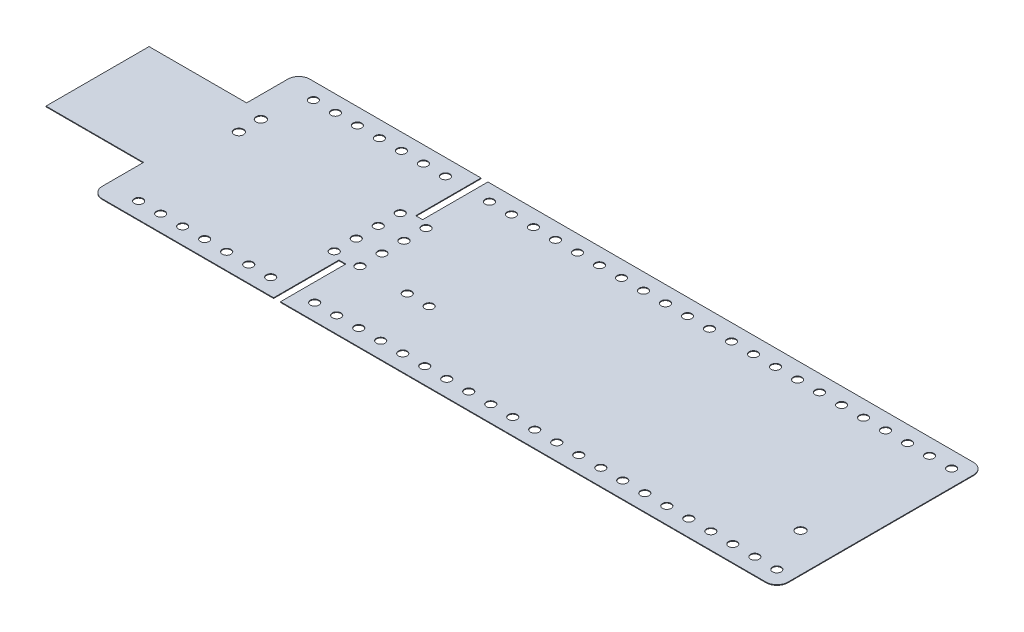
SolidWorks part; units mm, degrees
ref_plane "Front Plane" through (0, 0, 0) normal (0, 0, 1) x (1, 0, 0)
ref_plane "Top Plane" through (0, 0, 0) normal (0, 1, 0) x (1, 0, 0)
ref_plane "Right Plane" through (0, 0, 0) normal (1, 0, 0) x (0, 0, -1)
sketch "Sketch1" plane through (0, 0, 0) normal (0, 1, 0) x (1, 0, 0)
  line L0 (91.11, -12.065) -> (11.35, -12.065)
  line L1 (11.35, -5.995) -> (0, -5.995)
  line L3 (11.35, 5.995) -> (0, 5.995)
  line L4 (0, -5.995) -> (0, 5.995)
  line L5 (11.35, -5.995) -> (0, 5.995) construction
  line L6 (11.35, 5.995) -> (0, -5.995) construction
  line L7 (91.11, -12.065) -> (91.11, 12.065)
  line L8 (11.35, -12.065) -> (11.35, -5.995)
  line L9 (91.11, 12.065) -> (11.35, 12.065)
  line L10 (91.11, -12.065) -> (11.35, 12.065) construction
  line L11 (11.35, -12.065) -> (91.11, 12.065) construction
  line L12 (11.35, 5.995) -> (11.35, 12.065)
  point P0 (5.675, 0)
  point P7 (51.23, 0)
  dimension "D1" = 79.76
  dimension "D2" = 24.13
  dimension "D3" = 11.35
  dimension "D4" = 11.99
extrude "Boss-Extrude1" add sketch "Sketch1" along normal mid plane 0.0787
sketch "Sketch2" plane through (0, 0.0394, 0) normal (0, 1, 0) x (1, 0, 0)
  line L0 (11.35, 10.165) -> (91.11, 10.165) construction
  line L1 (91.11, 12.065) -> (11.35, 12.065) construction
  line L2 (91.11, -12.065) -> (91.11, 12.065) construction
  line L3 (2.5568, -8.5055) -> (57.273, -8.5055) construction
  line L4 (11.35, 12.065) -> (11.35, 5.995) construction
  circle A0 centre (14.95, 10.165) radius 0.5
  circle A1 centre (17.51, 10.165) radius 0.5
  circle A2 centre (20.07, 10.165) radius 0.5
  circle A3 centre (22.63, 10.165) radius 0.5
  circle A4 centre (25.19, 10.165) radius 0.5
  circle A5 centre (27.75, 10.165) radius 0.5
  circle A6 centre (30.31, 10.165) radius 0.5
  circle A7 centre (32.87, 10.165) radius 0.5 [skipped]
  circle A8 centre (35.43, 10.165) radius 0.5
  circle A9 centre (37.99, 10.165) radius 0.5
  circle A10 centre (40.55, 10.165) radius 0.5
  circle A11 centre (43.11, 10.165) radius 0.5
  circle A12 centre (45.67, 10.165) radius 0.5
  circle A13 centre (48.23, 10.165) radius 0.5
  circle A14 centre (50.79, 10.165) radius 0.5
  circle A15 centre (53.35, 10.165) radius 0.5
  circle A16 centre (55.91, 10.165) radius 0.5
  circle A17 centre (58.47, 10.165) radius 0.5
  circle A18 centre (61.03, 10.165) radius 0.5
  circle A19 centre (63.59, 10.165) radius 0.5
  circle A20 centre (66.15, 10.165) radius 0.5
  circle A21 centre (68.71, 10.165) radius 0.5
  circle A22 centre (71.27, 10.165) radius 0.5
  circle A23 centre (73.83, 10.165) radius 0.5
  circle A24 centre (76.39, 10.165) radius 0.5
  circle A25 centre (78.95, 10.165) radius 0.5
  circle A26 centre (81.51, 10.165) radius 0.5
  circle A27 centre (84.07, 10.165) radius 0.5
  circle A28 centre (86.63, 10.165) radius 0.5
  circle A29 centre (89.19, 10.165) radius 0.5
  dimension "D1" = 1
  dimension "D2" = 1.9
  dimension "D3" = 3.6
  dimension "D4" = 30
extrude "Cut-Extrude1" cut sketch "Sketch2" against normal through all
mirror "Mirror1" about plane through (0, 0, 0) normal (0, 0, 1) of "Cut-Extrude1"
sketch "Sketch3" plane through (0, 0.0394, 0) normal (0, 1, 0) x (1, 0, 0)
  circle A0 centre (31.3965, 3.8201) radius 0.5
  circle A2 centre (34.3965, 3.8201) radius 0.5
  circle A3 centre (34.3965, 1.2601) radius 0.5
  circle A4 centre (34.3965, -1.2999) radius 0.5
  circle A5 centre (34.3965, -3.8599) radius 0.5
  circle A6 centre (31.3965, 1.2601) radius 0.5
  circle A7 centre (31.3965, -1.2999) radius 0.5
  circle A8 centre (31.3965, -3.8599) radius 0.5
  dimension "D1" = 1
  dimension "D2" = 2
  dimension "D3" = 4
extrude "Cut-Extrude2" cut sketch "Sketch3" against normal through all
sketch "Sketch4" plane through (0, 0.0394, 0) normal (0, 1, 0) x (1, 0, 0)
  circle A0 centre (39.8965, -3.8713) radius 0.5
  circle A1 centre (42.4565, -3.8713) radius 0.5
  dimension "D1" = 1
  dimension "D2" = 2.56
extrude "Cut-Extrude3" cut sketch "Sketch4" against normal through all
sketch "Sketch5" plane through (0, 0.0394, 0) normal (0, 1, 0) x (1, 0, 0)
  line L0 (91.11, 12.065) -> (11.35, 12.065) construction
  line L1 (32.55, 12.065) -> (33.35, 12.065)
  line L2 (32.55, 12.065) -> (32.55, 4.465)
  line L3 (32.55, 4.465) -> (33.35, 4.465)
  line L4 (33.35, 12.065) -> (33.35, 4.465)
  line L5 (11.35, 12.065) -> (11.35, 5.995) construction
  dimension "D1" = 0.8
  dimension "D2" = 21.2
  dimension "D3" = 7.6
extrude "Cut-Extrude4" cut sketch "Sketch5" against normal through all
mirror "Mirror2" about plane through (0, 0, 0) normal (0, 0, 1) of "Cut-Extrude4"
sketch "Sketch6" plane through (0, 0.0394, 0) normal (0, 1, 0) x (1, 0, 0)
  circle A0 centre (13.8275, 5.1743) radius 0.5461
  circle A1 centre (13.8275, 2.6143) radius 0.5461
  dimension "D1" = 1.0922
  dimension "D2" = 2.56
extrude "Cut-Extrude5" cut sketch "Sketch6" against normal through all
sketch "Sketch7" plane through (0, 0.0394, 0) normal (0, 1, 0) x (1, 0, 0)
  circle A0 centre (86.6546, -4.8663) radius 0.5461
  dimension "D1" = 1.0922
extrude "Cut-Extrude6" cut sketch "Sketch7" against normal through all
fillet "Fillet1" radius 1.27 4 edges at (91.11, 0, -12.065) (91.11, 0, 12.065) (11.35, 0, 12.065) (11.35, 0, -12.065)
